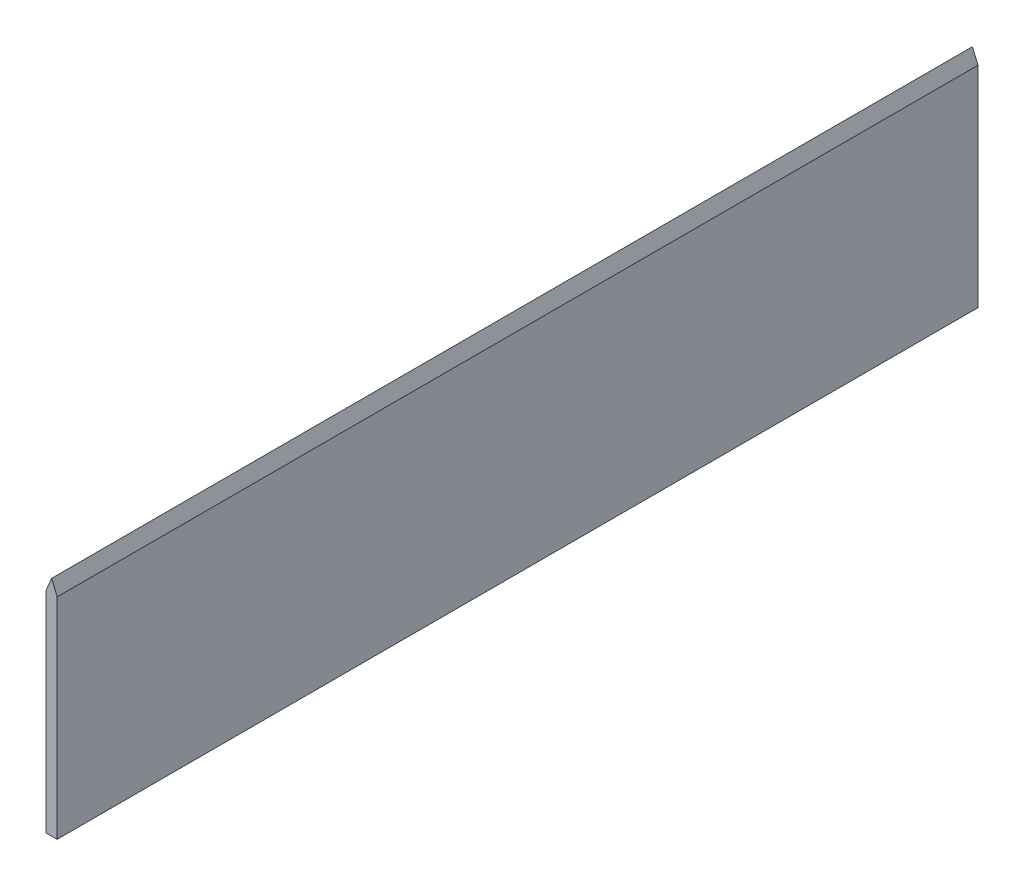
SolidWorks part; units mm, degrees
material "Balsa"
ref_plane "Front Plane" through (0, 0, 0) normal (0, 0, 1) x (1, 0, 0)
ref_plane "Top Plane" through (0, 0, 0) normal (0, 1, 0) x (1, 0, 0)
ref_plane "Right Plane" through (0, 0, 0) normal (1, 0, 0) x (0, 0, -1)
sketch "Sketch1" plane through (0, 0, 0) normal (0, 0, 1) x (1, 0, 0)
  line L1 (-2, 2.3791) -> (0, 2.3791)
  line L2 (-2, 2.3791) -> (-2, -37.6209)
  line L3 (-2, -37.6209) -> (0, -37.6209)
  line L4 (0, 2.3791) -> (0, -37.6209)
  dimension "D1" = 2
  dimension "D2" = 40
extrude "Boss-Extrude1" add sketch "Sketch1" along normal blind 165
sketch "Sketch2" plane through (0, 0, 165) normal (0, 0, 1) x (1, 0, 0)
  line L0 (-2, 2.3791) -> (-2, -0.1209)
  line L1 (-2, 2.3791) -> (-2, -37.6209) construction
  line L2 (-2, -0.1209) -> (-1, 2.3791)
  line L3 (0, 2.3791) -> (-2, 2.3791) construction
  line L4 (-1, 2.3791) -> (0, 0)
  line L5 (0, 0) -> (0, 2.3791)
  line L6 (-1, 2.3791) -> (0, 2.3791)
  line M3 (0, -37.6209) -> (0, 2.3791)
  line M4 (0, 2.3791) -> (-2, 2.3791)
extrude "Cut-Extrude1" cut sketch "Sketch2" against normal blind 165 contours L4 M4 M3
sketch "Sketch3" plane through (0, 0, 165) normal (0, 0, 1) x (1, 0, 0)
  line L0 (-1, 2.3791) -> (-2, 2.3791)
  line L1 (-2, 2.3791) -> (-2, 0)
  line L2 (-2, 2.3791) -> (-2, -37.6209) construction
  line L3 (-2, 0) -> (-1, 2.3791)
extrude "Cut-Extrude2" cut sketch "Sketch3" against normal blind 165
